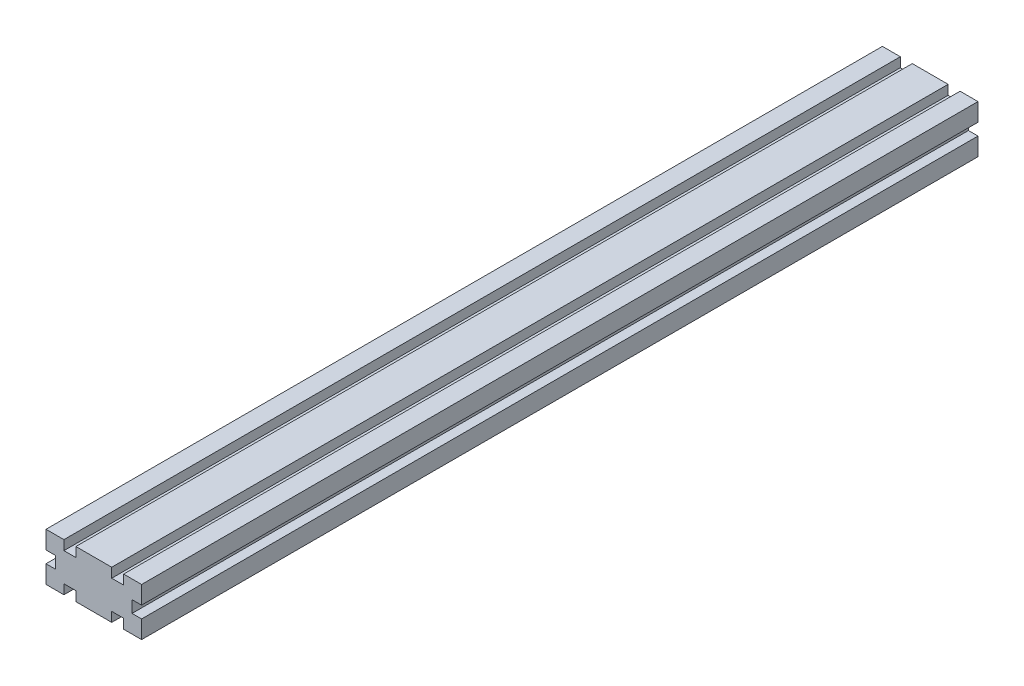
SolidWorks part; units mm, degrees
ref_plane "Plan de face" through (0, 0, 0) normal (0, 0, 1) x (1, 0, 0)
ref_plane "Plan de dessus" through (0, 0, 0) normal (0, 1, 0) x (1, 0, 0)
ref_plane "Plan de droite" through (0, 0, 0) normal (1, 0, 0) x (0, 0, -1)
sketch "Esquisse1" plane through (0, 0, 0) normal (0, 0, 1) x (1, 0, 0)
  line L0 (20, 20) -> (20, 0)
  line L1 (0, 0) -> (40, 0)
  line L2 (0, 0) -> (0, 20)
  line L3 (0, 20) -> (40, 20)
  line L4 (40, 0) -> (40, 20)
  line L5 (20, 0) -> (40, 20)
  line L6 (40, 0) -> (20, 20)
  line L7 (0, 0) -> (20, 20)
  line L8 (20, 0) -> (0, 20)
  line L10 (4, 4) -> (16, 4)
  line L11 (4, 4) -> (4, 16)
  line L12 (4, 16) -> (16, 16)
  line L13 (16, 4) -> (16, 16)
  line L14 (4, 4) -> (16, 16) construction
  line L15 (4, 16) -> (16, 4) construction
  line L16 (24, 4) -> (36, 4)
  line L17 (24, 4) -> (24, 16)
  line L18 (24, 16) -> (36, 16)
  line L19 (36, 4) -> (36, 16)
  line L20 (24, 4) -> (36, 16) construction
  line L21 (24, 16) -> (36, 4) construction
  line L22 (12.5, 0) -> (7.5, 0)
  line L23 (12.5, 0) -> (12.5, 20)
  line L24 (12.5, 20) -> (7.5, 20)
  line L25 (7.5, 0) -> (7.5, 20)
  line L26 (12.5, 0) -> (7.5, 20) construction
  line L27 (12.5, 20) -> (7.5, 0) construction
  line L28 (32.5, 0) -> (27.5, 0)
  line L29 (32.5, 0) -> (32.5, 20)
  line L30 (32.5, 20) -> (27.5, 20)
  line L31 (27.5, 0) -> (27.5, 20)
  line L32 (32.5, 0) -> (27.5, 20) construction
  line L33 (32.5, 20) -> (27.5, 0) construction
  line L34 (0, 7.5) -> (40, 7.5)
  line L35 (0, 7.5) -> (0, 12.5)
  line L36 (0, 12.5) -> (40, 12.5)
  line L37 (40, 7.5) -> (40, 12.5)
  line L38 (0, 7.5) -> (40, 12.5) construction
  line L39 (0, 12.5) -> (40, 7.5) construction
  point P7 (10, 10)
  point P12 (30, 10)
  point P17 (10, 10)
  point P22 (30, 10)
  point P27 (20, 10)
  dimension "D1" = 20
  dimension "D2" = 40
  dimension "D3" = 12
  dimension "D5" = 5
  dimension "D6" = 5
  dimension "D7" = 5
extrude "Boss.-Extru.1" add sketch "Esquisse1" along normal blind 350 contours L12 L25 L3 L8 | L2 L36 L11 L8 | L34 L2 L7 L11 | L1 L25 L10 L7 | L34 L11 L7 | L10 L25 L7 | L11 L36 L8 | L8 L25 L12 | L36 L11 L34 L25 | L25 L7 L8 | L36 L8 L7 | L8 L23 L7 | L7 L34 L8 | L23 L10 L8 | L34 L8 L13 | L34 L13 L8 L0 | L25 L36 L23 L12 | L36 L23 L34 L13 | L23 L7 L12 | L23 L12 L7 L3 | L7 L36 L13 | L13 L36 L0 L7 | L23 L1 L8 L10 | L34 L25 L10 L23 | L36 L13 L34 L0 | L36 L0 L34 L17 | L0 L36 L17 L6 | L18 L31 L3 L6 | L17 L36 L6 | L6 L31 L18 | L36 L17 L34 L31 | L34 L17 L5 | L34 L0 L5 L17 | L1 L31 L16 L5 | L16 L31 L5 | L34 L31 L16 L29 | L29 L16 L6 | L34 L6 L19 | L34 L19 L6 L4 | L29 L1 L6 L16 | L36 L29 L34 L19 | L6 L29 L5 | L5 L34 L6 | L31 L5 L6 | L36 L6 L5 | L5 L36 L19 | L29 L5 L18 | L29 L18 L5 L3 | L19 L36 L4 L5 | L31 L36 L29 L18
